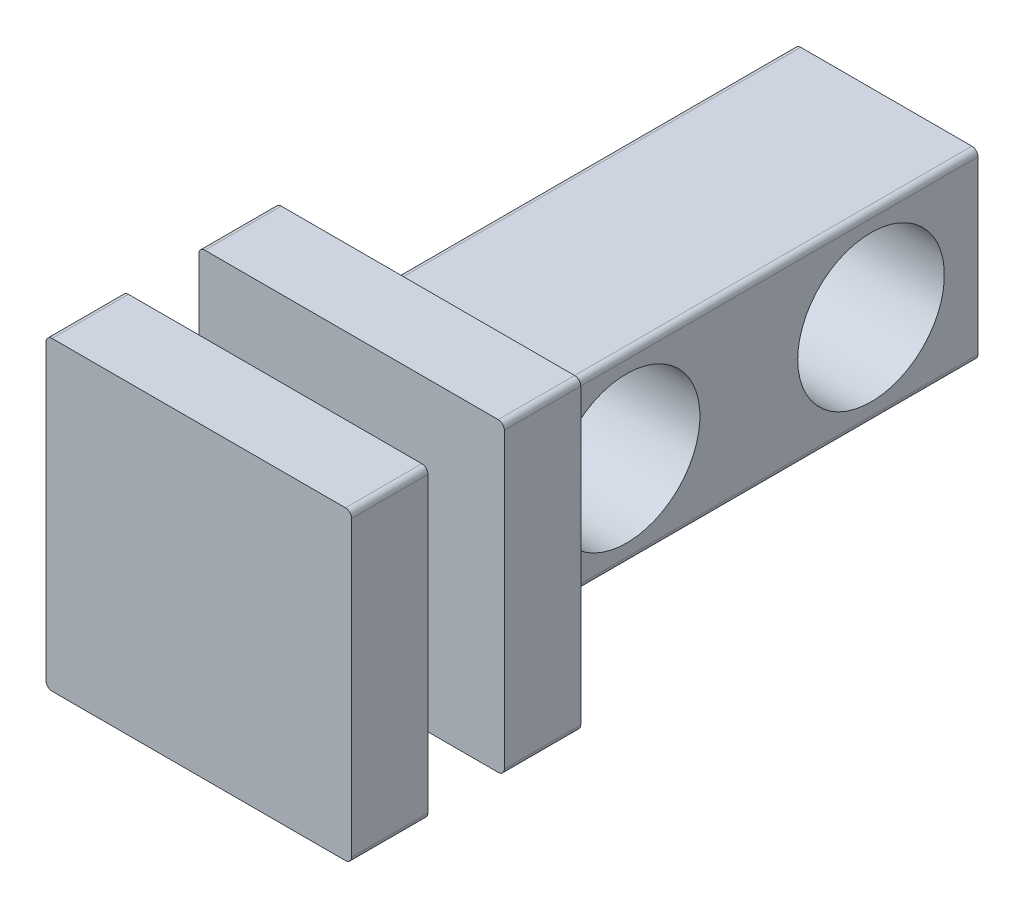
SolidWorks part; units mm, degrees
ref_plane "Front Plane" through (0, 0, 0) normal (0, 0, 1) x (1, 0, 0)
ref_plane "Top Plane" through (0, 0, 0) normal (0, 1, 0) x (1, 0, 0)
ref_plane "Right Plane" through (0, 0, 0) normal (1, 0, 0) x (0, 0, -1)
sketch "Sketch1" plane through (0, 0, 0) normal (0, 0, 1) x (1, 0, 0)
  line L1 (-1.778, -1.905) -> (1.778, -1.905)
  line L2 (-1.905, -1.778) -> (-1.905, 1.778)
  line L3 (-1.778, 1.905) -> (1.778, 1.905)
  line L4 (1.905, -1.778) -> (1.905, 1.778)
  line L5 (-1.905, -1.905) -> (1.905, 1.905) construction
  line L6 (-1.905, 1.905) -> (1.905, -1.905) construction
  arc A0 (-1.778, -1.905) -> (-1.905, -1.778) centre (-1.778, -1.778) cw
  arc A1 (1.778, -1.905) -> (1.905, -1.778) centre (1.778, -1.778) ccw
  arc A2 (1.778, 1.905) -> (1.905, 1.778) centre (1.778, 1.778) cw
  arc A3 (-1.905, 1.778) -> (-1.778, 1.905) centre (-1.778, 1.778) cw
  point P0 (0, 0)
  dimension "D3" = 0.127
  dimension "D1" = 3.81
  dimension "D2" = 3.81
extrude "Boss-Extrude1" add sketch "Sketch1" along normal blind 9.525
sketch "Sketch2" plane through (0, 0, 9.525) normal (0, 0, 1) x (1, 0, 0)
  line L1 (-3.048, -3.175) -> (3.048, -3.175)
  line L2 (-3.175, -3.048) -> (-3.175, 3.048)
  line L3 (-3.048, 3.175) -> (3.048, 3.175)
  line L4 (3.175, -3.048) -> (3.175, 3.048)
  line L5 (-3.175, -3.175) -> (3.175, 3.175) construction
  line L6 (-3.175, 3.175) -> (3.175, -3.175) construction
  arc A0 (-3.048, -3.175) -> (-3.175, -3.048) centre (-3.048, -3.048) cw
  arc A1 (3.048, -3.175) -> (3.175, -3.048) centre (3.048, -3.048) ccw
  arc A2 (3.048, 3.175) -> (3.175, 3.048) centre (3.048, 3.048) cw
  arc A3 (-3.175, 3.048) -> (-3.048, 3.175) centre (-3.048, 3.048) cw
  point P0 (0, 0)
  dimension "D3" = 0.127
  dimension "D1" = 6.35
  dimension "D2" = 6.35
extrude "Boss-Extrude2" add sketch "Sketch2" along normal blind 1.5875
sketch "Sketch3" plane through (0, 0, 11.1125) normal (0, 0, 1) x (1, 0, 0)
  line L1 (-1.4605, -1.5875) -> (1.4605, -1.5875)
  line L2 (-1.5875, -1.4605) -> (-1.5875, 1.4605)
  line L3 (-1.4605, 1.5875) -> (1.4605, 1.5875)
  line L4 (1.5875, -1.4605) -> (1.5875, 1.4605)
  line L5 (-1.5875, -1.5875) -> (1.5875, 1.5875) construction
  line L6 (-1.5875, 1.5875) -> (1.5875, -1.5875) construction
  arc A0 (-1.4605, -1.5875) -> (-1.5875, -1.4605) centre (-1.4605, -1.4605) cw
  arc A1 (1.4605, -1.5875) -> (1.5875, -1.4605) centre (1.4605, -1.4605) ccw
  arc A2 (1.4605, 1.5875) -> (1.5875, 1.4605) centre (1.4605, 1.4605) cw
  arc A3 (-1.5875, 1.4605) -> (-1.4605, 1.5875) centre (-1.4605, 1.4605) cw
  point P0 (0, 0)
  dimension "D3" = 0.127
  dimension "D1" = 3.175
  dimension "D2" = 3.175
extrude "Boss-Extrude3" add sketch "Sketch3" along normal blind 1.5875
sketch "Sketch4" plane through (0, 0, 12.7) normal (0, 0, 1) x (1, 0, 0)
  line L1 (-3.048, -3.175) -> (3.048, -3.175)
  line L2 (-3.175, -3.048) -> (-3.175, 3.048)
  line L3 (-3.048, 3.175) -> (3.048, 3.175)
  line L4 (3.175, -3.048) -> (3.175, 3.048)
  line L5 (-3.175, -3.175) -> (3.175, 3.175) construction
  line L6 (-3.175, 3.175) -> (3.175, -3.175) construction
  arc A0 (-3.048, -3.175) -> (-3.175, -3.048) centre (-3.048, -3.048) cw
  arc A1 (3.048, -3.175) -> (3.175, -3.048) centre (3.048, -3.048) ccw
  arc A2 (3.048, 3.175) -> (3.175, 3.048) centre (3.048, 3.048) cw
  arc A3 (-3.175, 3.048) -> (-3.048, 3.175) centre (-3.048, 3.048) cw
  point P0 (0, 0)
  dimension "D3" = 0.127
  dimension "D1" = 6.35
  dimension "D2" = 6.35
extrude "Boss-Extrude4" add sketch "Sketch4" along normal blind 1.5875
sketch "Sketch5" plane through (-1.905, 0, 0) normal (-1, 0, 0) x (0, 0, 1)
  line L0 (0, 1.778) -> (0, -1.778) construction
  circle A0 centre (2.2225, 0) radius 1.524
  circle A1 centre (7.3025, 0) radius 1.524
  point P0 (4.7625, 0)
  dimension "D2" = 3.048
  dimension "D3" = 3.048
  dimension "D1" = 4.7625
  dimension "D4" = 2.54
  dimension "D5" = 2.54
extrude "Cut-Extrude1" cut sketch "Sketch5" against normal through all
